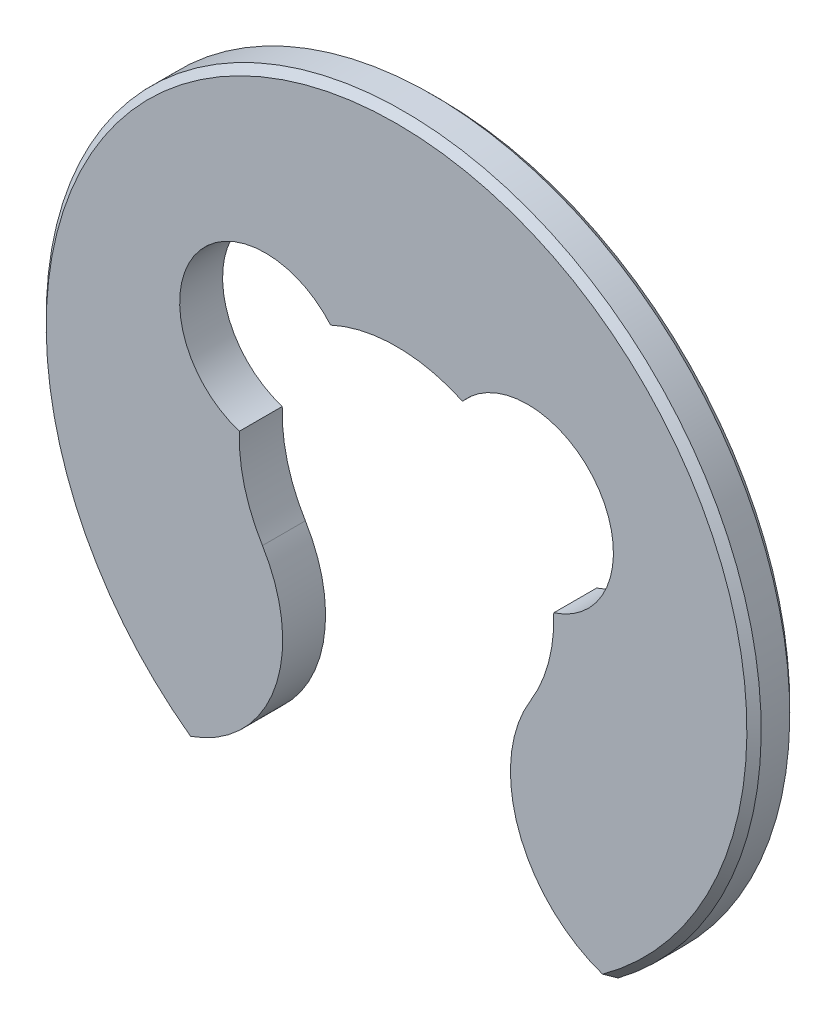
SolidWorks part; units mm, degrees
ref_plane "前视基准面" through (0, 0, 0) normal (0, 0, 1) x (1, 0, 0)
ref_plane "上视基准面" through (0, 0, 0) normal (0, 1, 0) x (1, 0, 0)
ref_plane "右视基准面" through (0, 0, 0) normal (1, 0, 0) x (0, 0, -1)
sketch "草图1" plane through (0, 0, 0) normal (0, 0, 1) x (1, 0, 0)
  line L0 (0, 2.0518) -> (0, -3.5323) construction
  arc A0 (-1.0994, 0.0365) -> (-0.9377, -0.575) centre (0, 0) ccw
  arc A1 (1.5, -2) -> (-1.5, -2) centre (0, 0) ccw
  arc A2 (-0.4612, 0.9986) -> (-1.0994, 0.0365) centre (-0.9167, 0.608) ccw
  arc A3 (1.0994, 0.0365) -> (0.4612, 0.9986) centre (0.9167, 0.608) ccw
  arc A4 (-0.9377, -0.575) -> (-1.5, -2) centre (-1.7548, -1.076) cw
  arc A5 (0.9377, -0.575) -> (1.5, -2) centre (1.7548, -1.076) ccw
  arc A6 (0.4612, 0.9986) -> (-0.4612, 0.9986) centre (0, 0) ccw
  arc A7 (0.9377, -0.575) -> (1.0994, 0.0365) centre (0, 0) ccw
  dimension "D1" = 1.1
  dimension "D2" = 5
  dimension "D3" = 0.6
  dimension "D6" = 3
extrude "凸台-拉伸1" add sketch "草图1" along normal blind 0.3
chamfer "倒角1" distance 0.05 angle 45 2 edges at (0, 2.5, 0.3) (0, 2.5, 0)
